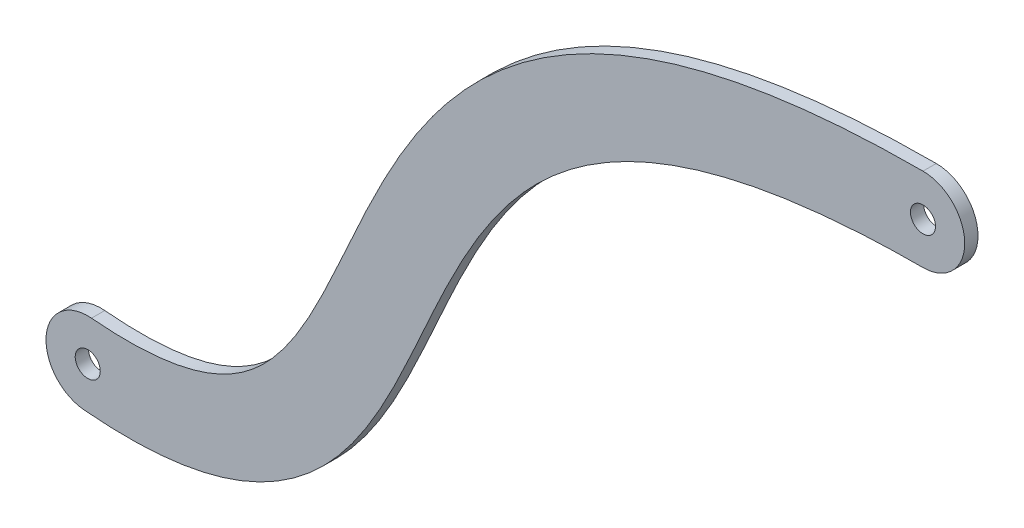
SolidWorks part; units mm, degrees
material "3D_printed_PLA"
ref_plane "Front Plane" through (0, 0, 0) normal (0, 0, 1) x (1, 0, 0)
ref_plane "Top Plane" through (0, 0, 0) normal (0, 1, 0) x (1, 0, 0)
ref_plane "Right Plane" through (0, 0, 0) normal (1, 0, 0) x (0, 0, -1)
sketch "Sketch2" plane through (0, 0, 0) normal (0, 0, 1) x (1, 0, 0)
  line L2 (-200, -130) -> (-122.6844, -130) construction
  line L3 (-122.6844, -130) -> (-122.6844, 0) construction
  line L4 (-122.6844, 0) -> (0, 0) construction
  arc A2 (0, 10) -> (0, -10) centre (0, 0) cw
  arc A3 (-199.0966, -120.0409) -> (-200.9034, -139.9591) centre (-200, -130) ccw
  circle A4 centre (0, 0) radius 3
  circle A5 centre (-200, -130) radius 3
  spline S0 degree 3 poles (0, 0) (-167.609, 0) (-96.3415, -139.4028) (-200, -130) knots 0 0 0 0 1 1 1 1 construction
  spline S1 degree 1 poles (0, 10) (-199.0966, -120.0409) knots 0 0 1 1 construction
  spline S2 degree 3 poles (0, 10) (-1.3389, 10) (-4.0366, 9.9824) (-9.2719, 9.8778) (-15.6299, 9.6186) (-22.9366, 9.1073) (-32.2737, 8.1652) (-43.2031, 6.5122) (-55.2042, 3.8074) (-66.1554, 0.4211) (-79.4334, -4.9444) (-93.6756, -13.1279) (-107.3586, -24.7933) (-118.0799, -37.6377) (-126.4511, -50.9979) (-133.1667, -64.3059) (-138.9074, -77.0656) (-144.2883, -88.799) (-149.8247, -99.0276) (-155.8982, -107.3286) (-161.6694, -112.5273) (-167.0836, -115.7691) (-171.7084, -117.7565) (-177.0652, -119.271) (-182.2678, -120.0803) (-186.9335, -120.4094) (-190.694, -120.4851) (-194.0612, -120.3949) (-196.8835, -120.2267) (-198.3654, -120.1072) (-199.0966, -120.0409) knots 0 0 0 0 0.007812 0.015625 0.03125 0.046875 0.0625 0.09375 0.125 0.15625 0.1875 0.25 0.3125 0.375 0.4375 0.5 0.5625 0.625 0.6875 0.75 0.8125 0.84375 0.875 0.90625 0.9375 0.953125 0.96875 0.984375 0.992188 1 1 1 1
  spline S3 degree 1 poles (0, -10) (-200.9034, -139.9591) knots 0 0 1 1 construction
  spline S4 degree 3 poles (0, -10) (-1.251, -10) (-3.7748, -10.0165) (-8.6477, -10.1139) (-14.5353, -10.3542) (-21.2459, -10.8243) (-29.7466, -11.6826) (-39.5525, -13.1691) (-50.0898, -15.5487) (-59.4837, -18.4583) (-70.6102, -22.9617) (-82.1486, -29.6155) (-93.054, -38.9117) (-101.7854, -49.3417) (-108.9435, -60.7242) (-115.0459, -72.7829) (-120.6245, -85.1696) (-126.2763, -97.5177) (-132.6985, -109.4616) (-140.7216, -120.5796) (-149.4896, -128.5653) (-157.9881, -133.6499) (-165.09, -136.6912) (-172.9039, -138.8837) (-180.0056, -139.9743) (-186.0581, -140.3987) (-190.7887, -140.4921) (-194.9029, -140.3808) (-198.29, -140.1786) (-200.0375, -140.0377) (-200.9034, -139.9591) knots 0 0 0 0 0.007812 0.015625 0.03125 0.046875 0.0625 0.09375 0.125 0.15625 0.1875 0.25 0.3125 0.375 0.4375 0.5 0.5625 0.625 0.6875 0.75 0.8125 0.84375 0.875 0.90625 0.9375 0.953125 0.96875 0.984375 0.992188 1 1 1 1
  dimension "D2" = 10
  dimension "D5" = 6
  dimension "D1" = 10
  dimension "D3" = 130
  dimension "D4" = 200
extrude "Boss-Extrude1" add sketch "Sketch2" along normal blind 3.175
